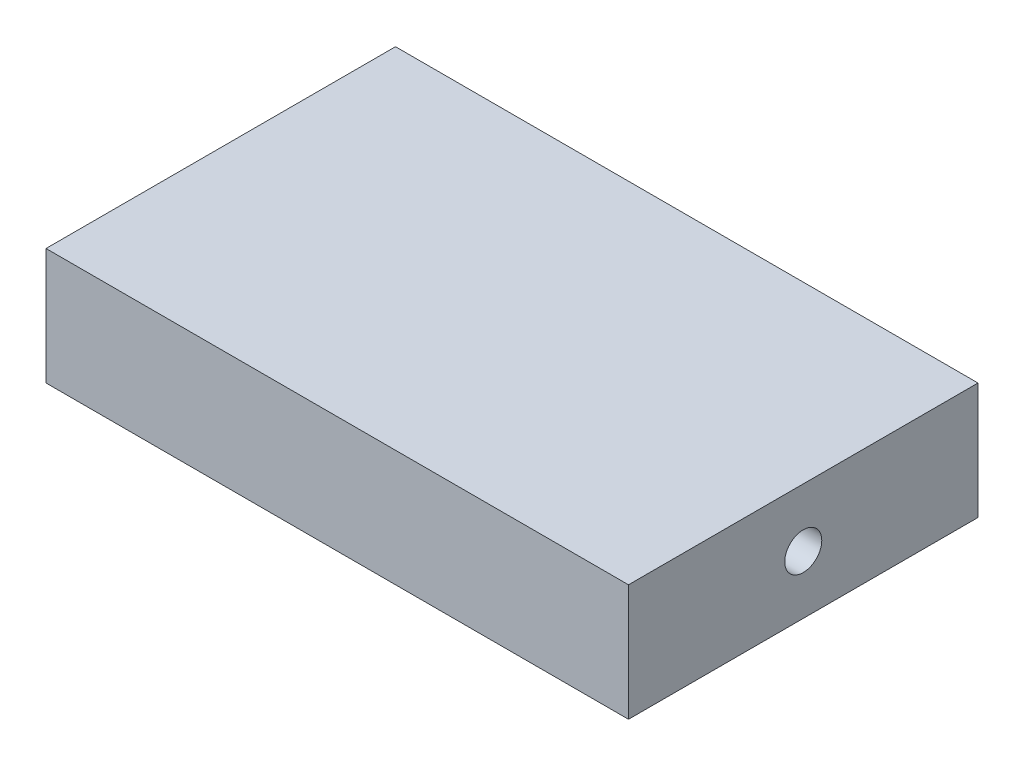
SolidWorks part; units mm, degrees
material "Plain Carbon Steel"
ref_plane "Front Plane" through (0, 0, 0) normal (0, 0, 1) x (1, 0, 0)
ref_plane "Top Plane" through (0, 0, 0) normal (0, 1, 0) x (1, 0, 0)
ref_plane "Right Plane" through (0, 0, 0) normal (1, 0, 0) x (0, 0, -1)
sketch "Sketch1" plane through (0, 0, 0) normal (0, 1, 0) x (1, 0, 0)
  line L1 (-31.75, -19.05) -> (31.75, -19.05)
  line L2 (-31.75, -19.05) -> (-31.75, 19.05)
  line L3 (-31.75, 19.05) -> (31.75, 19.05)
  line L4 (31.75, -19.05) -> (31.75, 19.05)
  line L5 (-31.75, -19.05) -> (31.75, 19.05) construction
  line L6 (-31.75, 19.05) -> (31.75, -19.05) construction
  point P0 (0, 0)
  dimension "D1" = 63.5
  dimension "D2" = 38.1
extrude "Boss-Extrude1" add sketch "Sketch1" along normal blind 12.7
sketch "Sketch2" plane through (0, 12.7, 0) normal (0, 1, 0) x (1, 0, 0)
  line L0 (31.75, -19.05) -> (31.75, 19.05) construction
  line L1 (-31.75, 19.05) -> (31.75, 19.05)
  line L2 (-31.75, 19.05) -> (-31.75, 6.35)
  line L3 (-31.75, 6.35) -> (31.75, 6.35)
  line L4 (31.75, 19.05) -> (31.75, 6.35)
  line L5 (-31.75, 19.05) -> (-31.75, -19.05) construction
  line L6 (31.75, -19.05) -> (-31.75, -19.05)
  line L7 (31.75, -19.05) -> (31.75, -6.35)
  line L8 (31.75, -6.35) -> (-31.75, -6.35)
  line L9 (-31.75, -19.05) -> (-31.75, -6.35)
  dimension "D1" = 12.7
  dimension "D2" = 12.7
extrude "Boss-Extrude2" [suppressed] add sketch "Sketch2" along normal blind 1.016 separate body
sketch "Sketch3" plane through (-31.75, 0, 0) normal (-1, 0, 0) x (0, 0, 1)
  line L0 (-19.05, 12.7) -> (19.05, 0) construction
  line L1 (19.05, 12.7) -> (-19.05, 0) construction
  point P8 (0, 6.35)
hole_wizard "#10-32 Tapped Hole1" positions "Sketch4" profile "Sketch5" tap size "#10-32" standard "ANSI Inch"
sketch "Sketch4" plane through (-31.75, 0, 0) normal (-1, 0, 0) x (0, 0, 1)
  point P0 (0, 6.35)
sketch "Sketch5" plane through (-31.75, 6.35, 0) normal (0, 1, 0) x (0, 0, 1)
  line L0 (0, 0) -> (0, 13.1513)
  line L1 (0, 13.1513) -> (2.0193, 11.938)
  line L2 (2.0193, 11.938) -> (2.0193, 0)
  line L5 (2.0193, 0) -> (0, 0)
  line L10 (0, 13.1513) -> (-2.0193, 11.938) construction
  line L11 (0, -6.35) -> (0, 107.95) construction
  dimension "Tap Drill Dia." = 4.0386
  dimension "Tap Drill Depth" = 11.938
  dimension "Drill Angle" = 118
mirror "Mirror1" about plane through (0, 0, 0) normal (1, 0, 0) of "#10-32 Tapped Hole1"
